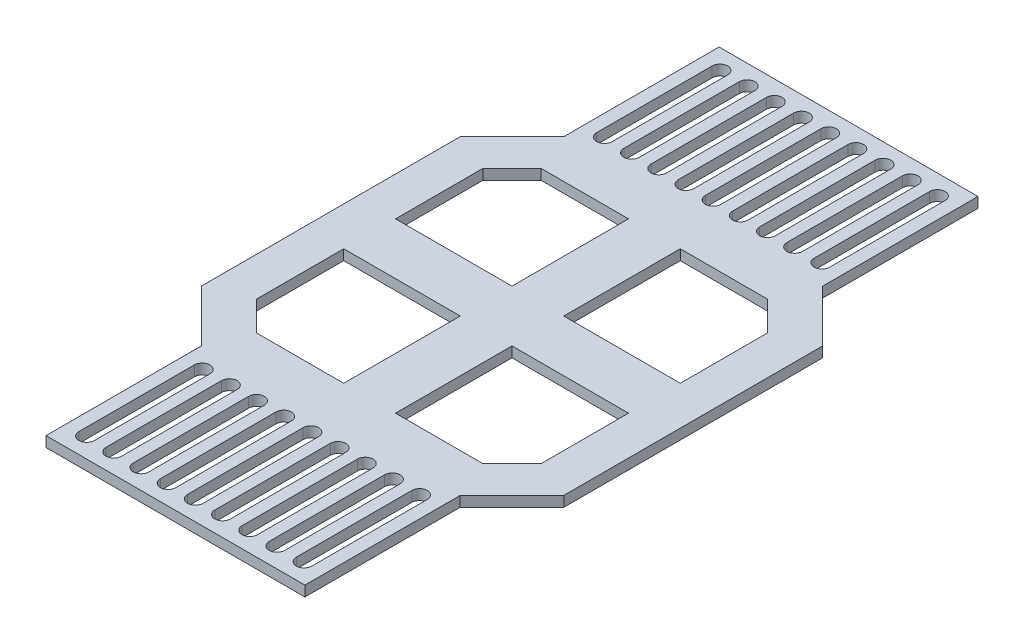
SolidWorks part; units mm, degrees
material "Thornel VCB-20 Carbon Cloth"
ref_plane "Front Plane" through (0, 0, 0) normal (0, 0, 1) x (1, 0, 0)
ref_plane "Top Plane" through (0, 0, 0) normal (0, 1, 0) x (1, 0, 0)
ref_plane "Right Plane" through (0, 0, 0) normal (1, 0, 0) x (0, 0, -1)
sketch "Sketch2" plane through (0, 0, 0) normal (0, 1, 0) x (1, 0, 0)
  line L0 (0, 65) -> (0, 35) construction
  line L1 (-35, 35) -> (-25, 35)
  line L2 (-35, 35) -> (-35, -35)
  line L3 (-35, -35) -> (-25, -35)
  line L4 (35, 35) -> (35, -35)
  line L5 (-35, 35) -> (35, -35) construction
  line L6 (-35, -35) -> (35, 35) construction
  line L7 (5.25, 38.8472) -> (5.25, 61.1528) construction
  line L8 (-25, 35) -> (-25, 65)
  line L9 (-25, 65) -> (25, 65)
  line L10 (25, 35) -> (25, 65)
  line L11 (0, 38.8472) -> (0, 61.1528) construction
  line L12 (-1.5, 38.8472) -> (-1.5, 61.1528)
  line L13 (1.5, 38.8472) -> (1.5, 61.1528)
  line L14 (25, 35) -> (35, 35)
  line L15 (3.75, 38.8472) -> (3.75, 61.1528)
  line L16 (6.75, 38.8472) -> (6.75, 61.1528)
  line L17 (10.5, 38.8472) -> (10.5, 61.1528) construction
  line L18 (9, 38.8472) -> (9, 61.1528)
  line L19 (12, 38.8472) -> (12, 61.1528)
  line L20 (15.75, 38.8472) -> (15.75, 61.1528) construction
  line L21 (14.25, 38.8472) -> (14.25, 61.1528)
  line L22 (17.25, 38.8472) -> (17.25, 61.1528)
  line L23 (21, 38.8472) -> (21, 61.1528) construction
  line L24 (19.5, 38.8472) -> (19.5, 61.1528)
  line L25 (22.5, 38.8472) -> (22.5, 61.1528)
  line L26 (-5.25, 38.8472) -> (-5.25, 61.1528) construction
  line L27 (-6.75, 38.8472) -> (-6.75, 61.1528)
  line L28 (-3.75, 38.8472) -> (-3.75, 61.1528)
  line L29 (-10.5, 38.8472) -> (-10.5, 61.1528) construction
  line L30 (-12, 38.8472) -> (-12, 61.1528)
  line L31 (-9, 38.8472) -> (-9, 61.1528)
  line L32 (-15.75, 38.8472) -> (-15.75, 61.1528) construction
  line L33 (-17.25, 38.8472) -> (-17.25, 61.1528)
  line L34 (-14.25, 38.8472) -> (-14.25, 61.1528)
  line L35 (-21, 38.8472) -> (-21, 61.1528) construction
  line L36 (-22.5, 38.8472) -> (-22.5, 61.1528)
  line L37 (-19.5, 38.8472) -> (-19.5, 61.1528)
  line L38 (0, -65) -> (0, 65) construction
  line L40 (-25, -35) -> (-25, -65)
  line L41 (-25, -65) -> (25, -65)
  line L42 (25, -35) -> (25, -65)
  line L43 (-35, 0) -> (35, 0) construction
  line L44 (5.25, -38.8472) -> (5.25, -61.1528) construction
  line L45 (3.75, -38.8472) -> (3.75, -61.1528)
  line L46 (6.75, -38.8472) -> (6.75, -61.1528)
  line L47 (0, -38.8472) -> (0, -61.1528) construction
  line L48 (-1.5, -38.8472) -> (-1.5, -61.1528)
  line L49 (1.5, -38.8472) -> (1.5, -61.1528)
  line L50 (10.5, -38.8472) -> (10.5, -61.1528) construction
  line L51 (9, -38.8472) -> (9, -61.1528)
  line L52 (12, -38.8472) -> (12, -61.1528)
  line L53 (15.75, -38.8472) -> (15.75, -61.1528) construction
  line L54 (14.25, -38.8472) -> (14.25, -61.1528)
  line L55 (17.25, -38.8472) -> (17.25, -61.1528)
  line L56 (21, -38.8472) -> (21, -61.1528) construction
  line L57 (19.5, -38.8472) -> (19.5, -61.1528)
  line L58 (22.5, -38.8472) -> (22.5, -61.1528)
  line L59 (-5.25, -38.8472) -> (-5.25, -61.1528) construction
  line L60 (-6.75, -38.8472) -> (-6.75, -61.1528)
  line L61 (-3.75, -38.8472) -> (-3.75, -61.1528)
  line L62 (-10.5, -38.8472) -> (-10.5, -61.1528) construction
  line L63 (-12, -38.8472) -> (-12, -61.1528)
  line L64 (-9, -38.8472) -> (-9, -61.1528)
  line L65 (-15.75, -38.8472) -> (-15.75, -61.1528) construction
  line L66 (-17.25, -38.8472) -> (-17.25, -61.1528)
  line L67 (-14.25, -38.8472) -> (-14.25, -61.1528)
  line L68 (-21, -38.8472) -> (-21, -61.1528) construction
  line L69 (-22.5, -38.8472) -> (-22.5, -61.1528)
  line L70 (-19.5, -38.8472) -> (-19.5, -61.1528)
  line L71 (25, -35) -> (35, -35)
  arc A0 (-1.5, 38.8472) -> (1.5, 38.8472) centre (0, 38.8472) ccw
  arc A1 (1.5, 61.1528) -> (-1.5, 61.1528) centre (0, 61.1528) ccw
  arc A2 (3.75, 38.8472) -> (6.75, 38.8472) centre (5.25, 38.8472) ccw
  arc A3 (6.75, 61.1528) -> (3.75, 61.1528) centre (5.25, 61.1528) ccw
  arc A4 (9, 38.8472) -> (12, 38.8472) centre (10.5, 38.8472) ccw
  arc A5 (12, 61.1528) -> (9, 61.1528) centre (10.5, 61.1528) ccw
  arc A6 (14.25, 38.8472) -> (17.25, 38.8472) centre (15.75, 38.8472) ccw
  arc A7 (17.25, 61.1528) -> (14.25, 61.1528) centre (15.75, 61.1528) ccw
  arc A8 (19.5, 38.8472) -> (22.5, 38.8472) centre (21, 38.8472) ccw
  arc A9 (22.5, 61.1528) -> (19.5, 61.1528) centre (21, 61.1528) ccw
  arc A10 (-6.75, 38.8472) -> (-3.75, 38.8472) centre (-5.25, 38.8472) ccw
  arc A11 (-3.75, 61.1528) -> (-6.75, 61.1528) centre (-5.25, 61.1528) ccw
  arc A12 (-12, 38.8472) -> (-9, 38.8472) centre (-10.5, 38.8472) ccw
  arc A13 (-9, 61.1528) -> (-12, 61.1528) centre (-10.5, 61.1528) ccw
  arc A14 (-17.25, 38.8472) -> (-14.25, 38.8472) centre (-15.75, 38.8472) ccw
  arc A15 (-14.25, 61.1528) -> (-17.25, 61.1528) centre (-15.75, 61.1528) ccw
  arc A16 (-22.5, 38.8472) -> (-19.5, 38.8472) centre (-21, 38.8472) ccw
  arc A17 (-19.5, 61.1528) -> (-22.5, 61.1528) centre (-21, 61.1528) ccw
  arc A18 (3.75, -38.8472) -> (6.75, -38.8472) centre (5.25, -38.8472) cw
  arc A19 (6.75, -61.1528) -> (3.75, -61.1528) centre (5.25, -61.1528) cw
  arc A20 (-1.5, -38.8472) -> (1.5, -38.8472) centre (0, -38.8472) cw
  arc A21 (1.5, -61.1528) -> (-1.5, -61.1528) centre (0, -61.1528) cw
  arc A22 (9, -38.8472) -> (12, -38.8472) centre (10.5, -38.8472) cw
  arc A23 (12, -61.1528) -> (9, -61.1528) centre (10.5, -61.1528) cw
  arc A24 (14.25, -38.8472) -> (17.25, -38.8472) centre (15.75, -38.8472) cw
  arc A25 (17.25, -61.1528) -> (14.25, -61.1528) centre (15.75, -61.1528) cw
  arc A26 (19.5, -38.8472) -> (22.5, -38.8472) centre (21, -38.8472) cw
  arc A27 (22.5, -61.1528) -> (19.5, -61.1528) centre (21, -61.1528) cw
  arc A28 (-6.75, -38.8472) -> (-3.75, -38.8472) centre (-5.25, -38.8472) cw
  arc A29 (-3.75, -61.1528) -> (-6.75, -61.1528) centre (-5.25, -61.1528) cw
  arc A30 (-12, -38.8472) -> (-9, -38.8472) centre (-10.5, -38.8472) cw
  arc A31 (-9, -61.1528) -> (-12, -61.1528) centre (-10.5, -61.1528) cw
  arc A32 (-17.25, -38.8472) -> (-14.25, -38.8472) centre (-15.75, -38.8472) cw
  arc A33 (-14.25, -61.1528) -> (-17.25, -61.1528) centre (-15.75, -61.1528) cw
  arc A34 (-22.5, -38.8472) -> (-19.5, -38.8472) centre (-21, -38.8472) cw
  arc A35 (-19.5, -61.1528) -> (-22.5, -61.1528) centre (-21, -61.1528) cw
  point P0 (0, 0)
  point P13 (0, 50)
  point P22 (5.25, 50)
  point P29 (10.5, 50)
  point P37 (15.75, 50)
  point P44 (21, 50)
  point P50 (-5.25, 50)
  point P57 (-10.5, 50)
  point P64 (-15.75, 50)
  point P71 (-21, 50)
  point P79 (0, -65)
  point P85 (5.25, -50)
  point P92 (0, -50)
  point P99 (10.5, -50)
  point P106 (15.75, -50)
  point P113 (21, -50)
  point P120 (-5.25, -50)
  point P127 (-10.5, -50)
  point P134 (-15.75, -50)
  point P141 (-21, -50)
  dimension "D5" = 3
  dimension "D6" = 5
  dimension "D7" = 5
  dimension "D9" = 50
  dimension "D1" = 70
  dimension "D2" = 70
  dimension "D3" = 50
  dimension "D4" = 30
  dimension "D8" = 30
extrude "Boss-Extrude1" add sketch "Sketch2" along normal blind 2
sketch "Sketch4" plane through (0, 0, 0) normal (0, -1, 0) x (1, 0, 0)
  line L0 (25, 35) -> (35, 25)
  line L1 (-35, 35) -> (-25, 35) construction
  line L2 (35, 35) -> (35, -35) construction
  line L3 (25, 35) -> (35, 35)
  line L4 (35, 35) -> (35, 25)
  line L5 (0, 0) -> (1.77, 0) construction
  line L6 (21.8934, 27.5) -> (27.5, 21.8934)
  line L7 (27.5, 21.8934) -> (27.5, 5)
  line L8 (27.5, 5) -> (5, 5)
  line L9 (5, 5) -> (5, 27.5)
  line L10 (5, 27.5) -> (21.8934, 27.5)
  line L11 (-30, -35) -> (-30, 35) construction
  line L12 (-25, -35) -> (-35, -35) construction
  line L13 (-35, 0) -> (35, 0) construction
  line L14 (-35, -35) -> (-35, 35) construction
  line L15 (0, 65) -> (0, -65) construction
  dimension "D1" = 45
  dimension "D2" = 7.5
  dimension "D3" = 7.5
  dimension "D4" = 5
  dimension "D5" = 5
  dimension "D6" = 7.5
  dimension "D7" = 25
extrude "Cut-Extrude1" cut sketch "Sketch4" against normal up to surface (2 mm away) up to face at (-15.75, 2, 50)
sketch "Sketch5" plane through (0, 0, 0) normal (1, 0, 0) x (0, 0, -1)
  line L0 (0, -0.174) -> (0, 0.9435) construction
pattern_circular "CirPattern1" count 4 over 360 about axis through (0, 0, 0) along (0, 1, 0) of "Cut-Extrude1"
